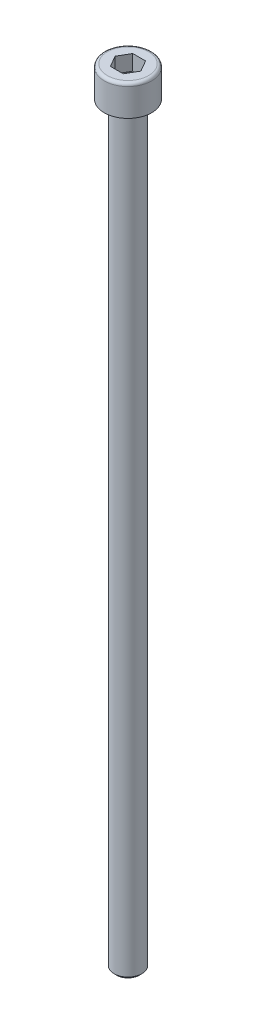
SolidWorks part; units mm, degrees
ref_plane "Plan1" through (0, 0, 0) normal (0, 0, 1) x (1, 0, 0)
ref_plane "Plan2" through (0, 0, 0) normal (0, 1, 0) x (1, 0, 0)
ref_plane "Plan3" through (0, 0, 0) normal (1, 0, 0) x (0, 0, -1)
sketch "Esquisse2" plane through (0, 0, 0) normal (0, 1, 0) x (1, 0, 0)
  circle A0 centre (0, 0) radius 2.5
  dimension "Diamètre nominal" = 5
extrude "Base-Extrusion" add sketch "Esquisse2" against normal blind 135
chamfer "Chanfrein1" distance 0.5 angle 45 1 edges at (0, -135, 2.5)
sketch "Esquisse5" plane through (0, 0, 0) normal (0, 0, 1) x (1, 0, 0)
  line L0 (-5.75, 0) -> (2.75, 0) construction
  line L1 (2, 5.5) -> (2, 2.75)
  line L2 (0, 0) -> (4.25, 0)
  line L3 (0, 0) -> (0, 1.5953)
  line L4 (2, 5.5) -> (3.7, 5.5)
  line L5 (4.25, 0) -> (4.25, 4.95)
  line L6 (2, 2.75) -> (0, 1.5953)
  line L7 (0, 5.5) -> (0, -135) construction
  line L8 (0, -134.5) -> (0, 0) construction
  line L9 (-2, -135) -> (2, -135) construction
  line L10 (2, 0) -> (-2, 0) construction
  arc A0 (4.25, 4.95) -> (3.7, 5.5) centre (3.7, 4.95) ccw
  dimension "D2" = 0.55
  dimension "D1" = 4.25
  dimension "Cote sur plats" = 4
  dimension "D3" = 60
  dimension "D4" = 2.75
  dimension "Diamètre tête" = 8.5
  dimension "Diamètre nominal" = 5.5
  dimension "D5" = 2
revolve "Boss.-Révol.1" add sketch "Esquisse5" angle 360 about L7
sketch "Esquisse7" plane through (0, 5.5, 0) normal (0, 1, 0) x (-1, 0, 0)
  line L0 (0, -2) -> (0, 2) construction
  line L1 (0, 0) -> (-1.1547, 2) construction
  line L2 (0, 0) -> (-1.7321, 1) construction
  line L3 (0, 0) -> (-2.3094, 0) construction
  line L4 (1.1547, 2) -> (-1.1547, 2)
  line L5 (-1.1547, 2) -> (-2.3094, 0)
  line L6 (1.1547, -2) -> (-1.1547, -2)
  line L7 (-1.1547, -2) -> (-2.3094, 0)
  line L8 (1.1547, 2) -> (2.3094, 0)
  line L9 (1.1547, -2) -> (2.3094, 0)
  circle A2 centre (0, 0) radius 2 construction
  dimension "D1" = 30
  dimension "D2" = 30
extrude "Enlèv. mat.-Extru.1" cut sketch "Esquisse7" against normal blind 2.75
equation "\"D1@Chanfrein1\" = \"Diamètre nominal@Esquisse2\"*0.1"
equation "\"D1@Esquisse5\" = \"Diamètre tête@Esquisse5\"/2"
equation "\"D2@Esquisse5\" = \"Diamètre nominal@Esquisse5\"*0.1"
equation "\"D4@Esquisse5\" = \"Diamètre nominal@Esquisse5\"/2"
equation "\"D5@Esquisse5\" = \"Cote sur plats@Esquisse5\"/2"
equation "\"D1@Enlèv. mat.-Extru.1\" = \"Diamètre nominal@Esquisse5\"/2"
